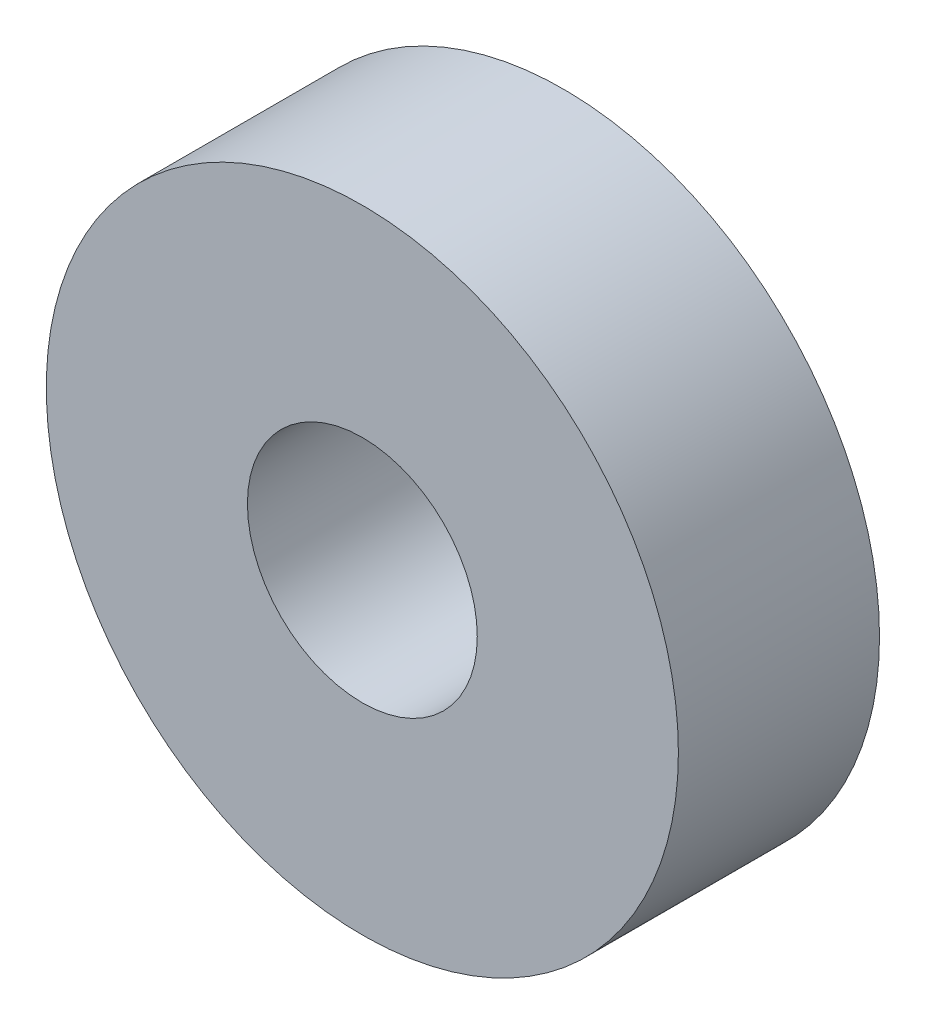
SolidWorks part; units mm, degrees
ref_plane "Front Plane" through (0, 0, 0) normal (0, 0, 1) x (1, 0, 0)
ref_plane "Top Plane" through (0, 0, 0) normal (0, 1, 0) x (1, 0, 0)
ref_plane "Right Plane" through (0, 0, 0) normal (1, 0, 0) x (0, 0, -1)
sketch "Sketch1" plane through (0, 0, 0) normal (0, 0, 1) x (1, 0, 0)
  circle A0 centre (0, 0) radius 11
  circle A1 centre (0, 0) radius 4
  dimension "D1" = 22
  dimension "D2" = 8
extrude "Boss-Extrude1" add sketch "Sketch1" along normal blind 7
